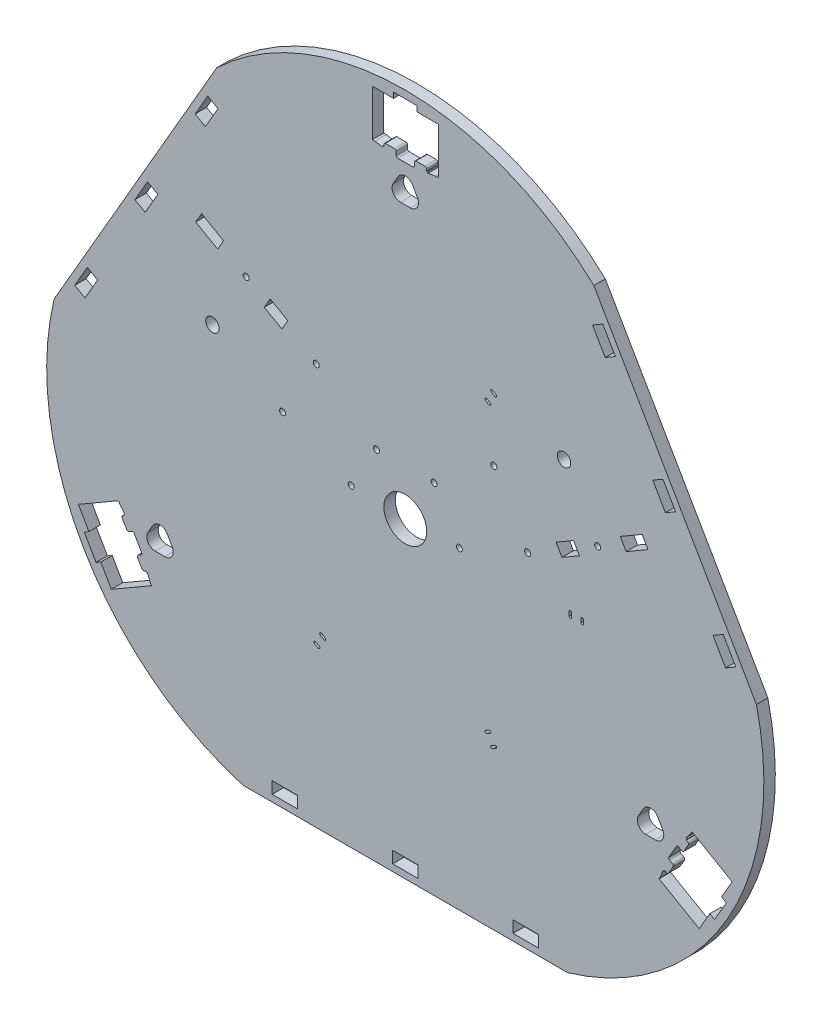
SolidWorks part; units mm, degrees
ref_plane "Front Plane" through (0, 0, 0) normal (0, 0, 1) x (1, 0, 0)
ref_plane "Top Plane" through (0, 0, 0) normal (0, 1, 0) x (1, 0, 0)
ref_plane "Right Plane" through (0, 0, 0) normal (1, 0, 0) x (0, 0, -1)
sketch "Sketch1" plane through (0, 0, 0) normal (0, 0, 1) x (1, 0, 0)
  line L0 (-96.5063, -185) -> (96.5063, -185)
  line L1 (208.4678, 8.9231) -> (111.9616, 176.0769)
  line L2 (-111.9616, 176.0769) -> (-208.4678, 8.9231)
  line L3 (0, 0) -> (-160.2147, 92.5) construction
  line L4 (0, 0) -> (160.2147, 92.5) construction
  line L5 (0, 0) -> (0, -185) construction
  arc A0 (-208.4678, 8.9231) -> (-96.5063, -185) centre (-49.8946, -28.8067) ccw
  arc A1 (96.5063, -185) -> (208.4678, 8.9231) centre (49.8946, -28.8067) ccw
  arc A2 (111.9616, 176.0769) -> (-111.9616, 176.0769) centre (0, 57.6133) ccw
  circle A3 centre (0, 0) radius 12.7
  dimension "D1" = 163
  dimension "D6" = 25.4
  dimension "D2" = 193.0125
  dimension "D3" = 60
  dimension "D4" = 185
  dimension "D5" = 120
extrude "Boss-Extrude1" add sketch "Sketch1" along normal blind 6.8
sketch "Sketch2" plane through (0, 0, 6.8) normal (0, 0, 1) x (1, 0, 0)
  line L0 (-96.5063, -185) -> (96.5063, -185) construction
  line L1 (-64, -181) -> (-79, -181)
  line L2 (-64, -181) -> (-64, -174)
  line L3 (-64, -174) -> (-79, -174)
  line L4 (-79, -181) -> (-79, -174)
  line L5 (-64, -181) -> (-79, -174) construction
  line L6 (-64, -174) -> (-79, -181) construction
  line L7 (7.5, -181) -> (-7.5, -181)
  line L8 (7.5, -181) -> (7.5, -174)
  line L9 (7.5, -174) -> (-7.5, -174)
  line L10 (-7.5, -181) -> (-7.5, -174)
  line L11 (7.5, -181) -> (-7.5, -174) construction
  line L12 (7.5, -174) -> (-7.5, -181) construction
  line L13 (79, -181) -> (64, -181)
  line L14 (79, -181) -> (79, -174)
  line L15 (79, -174) -> (64, -174)
  line L16 (64, -181) -> (64, -174)
  line L17 (79, -181) -> (64, -174) construction
  line L18 (79, -174) -> (64, -181) construction
  point P0 (-71.5, -177.5)
  point P5 (0, -177.5)
  point P10 (71.5, -177.5)
  dimension "D1" = 4
  dimension "D2" = 7
  dimension "D3" = 15
  dimension "D4" = 71.5
  dimension "D5" = 71.5
extrude "Cut-Extrude1" cut sketch "Sketch2" against normal blind 6.8
sketch "Sketch3" plane through (0, 0, 6.8) normal (0, 0, 1) x (1, 0, 0)
  line L1 (-12.7, 212.7) -> (12.7, 212.7) construction
  line L2 (-12.7, 212.7) -> (-12.7, 187.3) construction
  line L3 (0, 216.05) -> (7, 216.05)
  line L4 (7, 216.05) -> (7, 212.8)
  line L5 (7, 212.8) -> (19.58, 212.8)
  line L6 (19.58, 212.8) -> (19.58, 185.3)
  line L7 (19.58, 185.3) -> (18.08, 185.3)
  line L8 (18.08, 185.3) -> (13.536, 184.6)
  line L9 (13.536, 184.6) -> (13.2701, 185.3)
  line L10 (13.2701, 185.3) -> (12.7, 185.3)
  line L11 (12.7, 185.3) -> (12.7, 187.3)
  line L12 (12.7, 187.3) -> (5.45, 187.3)
  line L13 (5.45, 187.3) -> (5.45, 183.3)
  line L14 (5.45, 183.3) -> (0, 183.3)
  line L15 (0, 216.05) -> (0, 183.3)
  line L16 (-12.7, 187.3) -> (12.7, 187.3) construction
  line L17 (12.7, 212.7) -> (12.7, 187.3) construction
  line L18 (-12.7, 212.7) -> (12.7, 187.3) construction
  line L19 (-12.7, 187.3) -> (12.7, 212.7) construction
  point P0 (0, 200)
  dimension "D2" = 7
  dimension "D3" = 27.5
  dimension "D4" = 1.5
  dimension "D5" = 171.243
  dimension "D6" = 4.5976
  dimension "D7" = 102.046
  dimension "D8" = 6.88
  dimension "D9" = 7.25
  dimension "D10" = 4
  dimension "D11" = 19.58
  dimension "D12" = 25.4
  dimension "D13" = 25.5
  dimension "D14" = 3.25
  dimension "D15" = 200
extrude "Cut-Extrude2" cut sketch "Sketch3" against normal blind 6.8
mirror "Mirror1" about plane through (0, 0, 0) normal (1, 0, 0) of "Cut-Extrude2"
sketch "Sketch4" plane through (0, 0, 6.8) normal (0, 0, 1) x (1, 0, 0)
  line L0 (0, 171.5) -> (-2.9, 166.4771) construction
  line L1 (-2.9, 166.4771) -> (2.9, 166.4771) construction
  line L2 (2.9, 166.4771) -> (0, 171.5) construction
  line L3 (-2.9, 161.5271) -> (2.9, 161.5271)
  line L4 (7.1868, 168.9521) -> (4.2868, 173.975)
  line L5 (-4.2868, 173.975) -> (-7.1868, 168.9521)
  arc A0 (4.2868, 173.975) -> (-4.2868, 173.975) centre (0, 171.5) ccw
  arc A1 (2.9, 161.5271) -> (7.1868, 168.9521) centre (2.9, 166.4771) ccw
  arc A2 (-7.1868, 168.9521) -> (-2.9, 161.5271) centre (-2.9, 166.4771) ccw
  circle A3 centre (0, 0) radius 12.7 construction
  dimension "D1" = 9.9
  dimension "D2" = 5.8
  dimension "D3" = 171.5
extrude "Cut-Extrude3" cut sketch "Sketch4" against normal blind 6.8
fillet "Fillet1" radius 1 6 edges at (-12.7, 187.3, 3.4) (-5.45, 187.3, 3.4) (-5.45, 183.3, 3.4) (5.45, 183.3, 3.4) (5.45, 187.3, 3.4) (12.7, 187.3, 3.4)
pattern_circular "CirPattern1" count 3 over 360 about axis through (0, 0, 0) along (0, 0, 1) of "Cut-Extrude2", "Mirror1", "Cut-Extrude3", "Fillet1", "Cut-Extrude1"
sketch "Sketch5" plane through (0, 0, 6.8) normal (0, 0, 1) x (1, 0, 0)
  line L0 (0, 0) -> (-160.2147, 92.5) construction
  line L1 (-111.9616, 176.0769) -> (-208.4678, 8.9231) construction
  line L2 (-124.3769, 90.5729) -> (-111.3865, 83.0729)
  line L3 (-111.3865, 83.0729) -> (-107.8865, 89.1351)
  line L4 (-107.8865, 89.1351) -> (-120.8769, 96.6351)
  line L5 (-120.8769, 96.6351) -> (-124.3769, 90.5729)
  line L6 (-80.1737, 73.1351) -> (-69.7814, 67.1351)
  line L7 (-69.7814, 67.1351) -> (-73.2814, 61.0729)
  line L8 (-73.2814, 61.0729) -> (-83.6737, 67.0729)
  line L9 (-83.6737, 67.0729) -> (-80.1737, 73.1351)
  line L10 (-109.6365, 86.104) -> (-81.9237, 70.104) construction
  line L11 (-71.5314, 64.104) -> (-52.8599, 53.324) construction
  line L12 (-94.4811, 77.354) -> (-114.4811, 42.713) construction
  line L13 (-52.8599, 53.324) -> (-62.7349, 36.22) construction
  line L14 (-17.1131, 27.2008) -> (-32.1131, 1.22) construction
  line L15 (-62.7349, 36.22) -> (-72.8599, 18.683) construction
  circle A0 centre (-94.4811, 77.354) radius 1.775
  circle A1 centre (-52.8599, 53.324) radius 1.775
  circle A2 centre (-114.4811, 42.713) radius 4
  circle A3 centre (-72.8599, 18.683) radius 1.775
  circle A4 centre (-17.1131, 27.2008) radius 1.775
  circle A5 centre (-32.1131, 1.22) radius 1.775
  point P28 (-24.6131, 14.2104)
  dimension "D8" = 3.55
  dimension "D10" = 8
  dimension "D1" = 15
  dimension "D2" = 12
  dimension "D3" = 7
  dimension "D4" = 16.25
  dimension "D5" = 32
  dimension "D6" = 32
  dimension "D7" = 17.5
  dimension "D9" = 21.56
  dimension "D11" = 40
  dimension "D12" = 40
  dimension "D13" = 30
  dimension "D14" = 44.0192
extrude "Cut-Extrude4" cut sketch "Sketch5" against normal blind 6.8
pattern_circular "CirPattern2" count 3 over 360 about axis through (0, 0, 6.8) along (0, 0, 1) skipping 1 of "Cut-Extrude4"
sketch "Sketch6" plane through (0, 0, 6.8) normal (0, 0, 1) x (1, 0, 0)
  line L0 (0, 0) -> (0, 121.0871) construction
  line L1 (0, 0) -> (61.4865, 106.4978) construction
  line L2 (50.0392, 84.2705) -> (47.9608, 85.4705) construction
  line L3 (49.6642, 83.621) -> (47.5858, 84.821)
  line L4 (50.4142, 84.92) -> (48.3358, 86.12)
  line L5 (53.5392, 90.3327) -> (51.4608, 91.5327) construction
  line L6 (53.1642, 89.6831) -> (51.0858, 90.8831)
  line L7 (53.9142, 90.9822) -> (51.8358, 92.1822)
  arc A0 (49.6642, 83.621) -> (50.4142, 84.92) centre (50.0392, 84.2705) ccw
  arc A1 (48.3358, 86.12) -> (47.5858, 84.821) centre (47.9608, 85.4705) ccw
  arc A2 (53.1642, 89.6831) -> (53.9142, 90.9822) centre (53.5392, 90.3327) ccw
  arc A3 (51.8358, 92.1822) -> (51.0858, 90.8831) centre (51.4608, 91.5327) ccw
  point P6 (49, 84.8705)
  point P12 (52.5, 90.9327)
  dimension "D3" = 0.75
  dimension "D1" = 30
  dimension "D2" = 2.4
  dimension "D4" = 7
  dimension "D5" = 98
extrude "Cut-Extrude5" cut sketch "Sketch6" against normal blind 6.8
pattern_circular "CirPattern3" count 4 over 180 about axis through (0, 0, 0) along (0, 0, 1) of "Cut-Extrude5"
